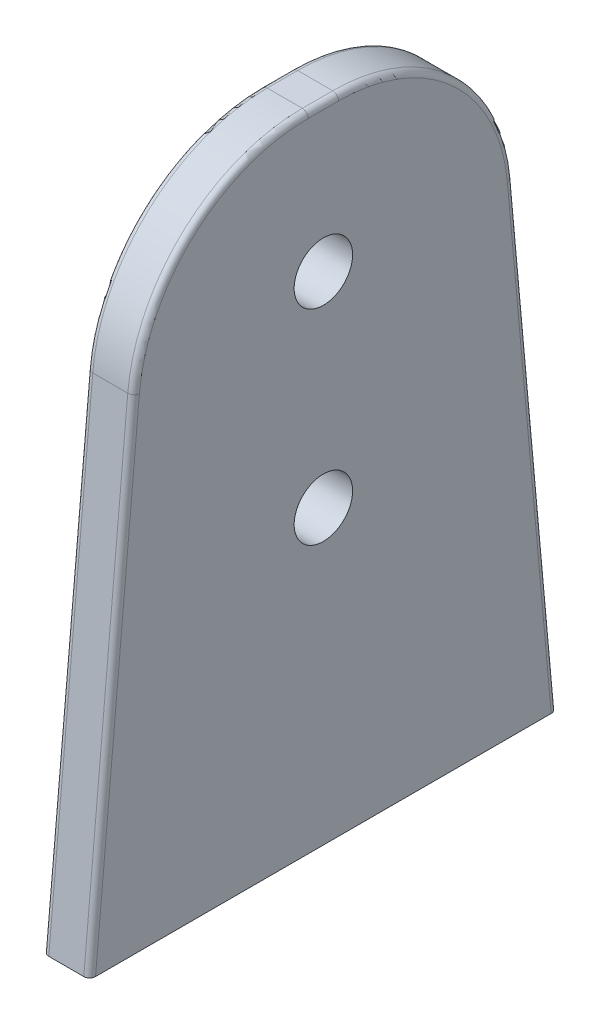
SolidWorks part; units mm, degrees
ref_plane "Přední rovina" through (0, 0, 0) normal (0, 0, 1) x (1, 0, 0)
ref_plane "Vrchní rovina" through (0, 0, 0) normal (0, 1, 0) x (1, 0, 0)
ref_plane "Pravá rovina" through (0, 0, 0) normal (1, 0, 0) x (0, 0, -1)
sketch "Skica1" plane through (0, 0, 0) normal (1, 0, 0) x (0, 0, -1)
  line L0 (0, 162.2344) -> (0, -8.318) construction
  line L1 (-30, 110) -> (30, 110)
  line L2 (30, 110) -> (40, 0)
  line L3 (40, 0) -> (-40, 0)
  line L4 (-30, 110) -> (-40, 0)
  circle A0 centre (0, 85) radius 5
  circle A1 centre (0, 50) radius 5
  point P8 (0, 55.5559)
  point P12 (0, 0)
  point P13 (0, 110)
  point P14 (0, 110.0563)
  point P15 (30, 89.5157)
  point P16 (0, 162.2344)
  point P17 (0, -20.1617)
  point P18 (0, -8.318)
  dimension "D1" = 10
  dimension "D2" = 80
  dimension "D3" = 110
  dimension "D4" = 50
  dimension "D5" = 35
  dimension "D6" = 60
extrude "Přidat vysunutím1" add sketch "Skica1" along normal blind 8
fillet "Zaoblit1" radius 30 2 edges at (4, 110, -30) (4, 110, 30)
fillet "Zaoblit2" radius 1 10 edges at (0, 41.358, -36.2402) (0, 102.1527, -22.8337) (0, 110, 0) (0, 102.1527, 22.8337) (8, 41.358, -36.2402) (8, 102.1527, -22.8337) (8, 110, 0) (8, 41.358, 36.2402) (0, 41.358, 36.2402) (8, 102.1527, 22.8337)
